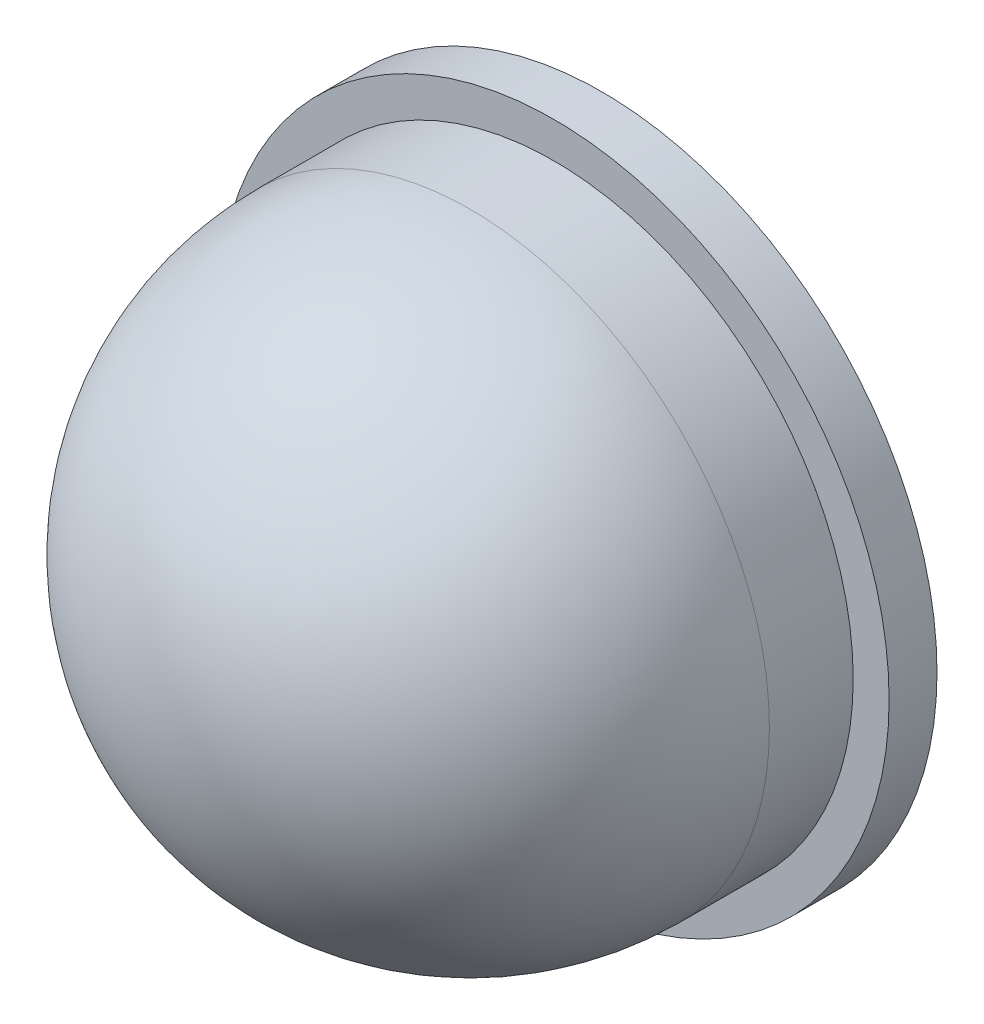
SolidWorks part; units mm, degrees
ref_plane "Front Plane" through (0, 0, 0) normal (0, 0, 1) x (1, 0, 0)
ref_plane "Top Plane" through (0, 0, 0) normal (0, 1, 0) x (1, 0, 0)
ref_plane "Right Plane" through (0, 0, 0) normal (1, 0, 0) x (0, 0, -1)
sketch "Sketch1" plane through (0, 0, 0) normal (0, 0, 1) x (1, 0, 0)
  circle A0 centre (0, 0) radius 12.5
  dimension "D1" = 25
extrude "Boss-Extrude1" add sketch "Sketch1" along normal blind 16
fillet "Fillet1" radius 12.5 1 edges at (12.5, 0, 16)
sketch "Sketch2" plane through (0, 0, 0) normal (0, 0, -1) x (-1, 0, 0)
  circle A0 centre (0, 0) radius 14
  dimension "D1" = 28
extrude "Boss-Extrude2" add sketch "Sketch2" along normal blind 2
